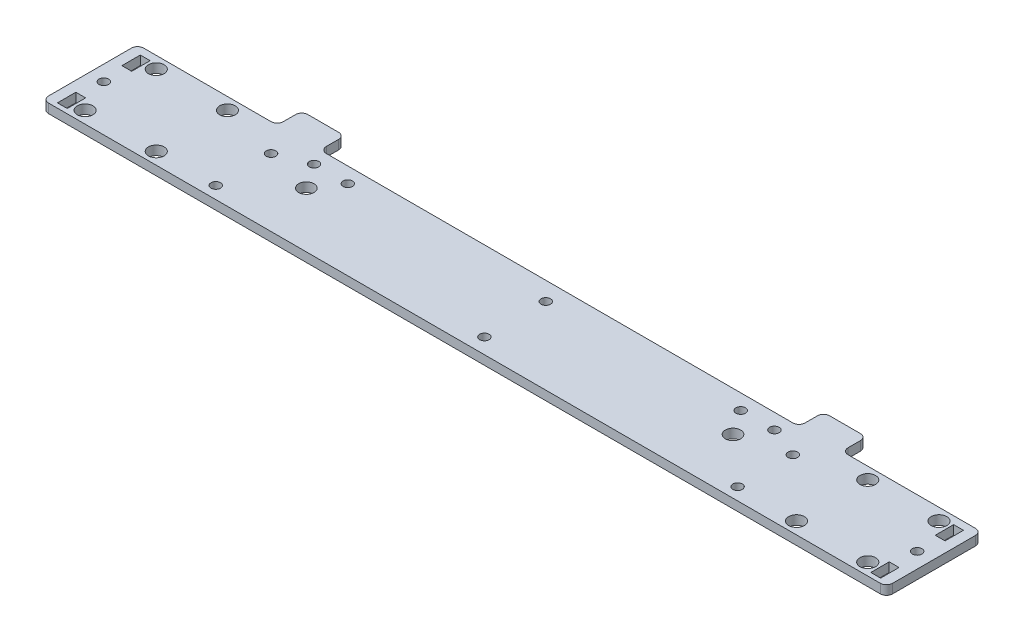
SolidWorks part; units mm, degrees
ref_plane "Alzado" through (0, 0, 0) normal (0, 0, 1) x (1, 0, 0)
ref_plane "Planta" through (0, 0, 0) normal (0, 1, 0) x (1, 0, 0)
ref_plane "Vista lateral" through (0, 0, 0) normal (1, 0, 0) x (0, 0, -1)
sketch "Croquis1" plane through (0, 0, 0) normal (0, 1, 0) x (1, 0, 0)
  line L0 (137.5, 31) -> (137.5, 0) construction
  line L1 (0, 0) -> (275, 0)
  line L2 (0, 0) -> (0, 31)
  line L3 (0, 31) -> (45.5, 31)
  line L4 (275, 0) -> (275, 31)
  line L5 (271.6, 1.5) -> (268.4, 1.5)
  line L6 (3.4, 28.5) -> (6.6, 28.5)
  line L7 (3.4, 28.5) -> (3.4, 22.5)
  line L8 (3.4, 22.5) -> (6.6, 22.5)
  line L9 (6.6, 28.5) -> (6.6, 22.5)
  line L10 (3.4, 7.5) -> (6.6, 7.5)
  line L11 (3.4, 7.5) -> (3.4, 1.5)
  line L12 (3.4, 1.5) -> (6.6, 1.5)
  line L13 (6.6, 7.5) -> (6.6, 1.5)
  line L14 (271.6, 7.5) -> (271.6, 1.5)
  line L15 (271.6, 7.5) -> (268.4, 7.5)
  line L16 (268.4, 7.5) -> (268.4, 1.5)
  line L17 (271.6, 22.5) -> (268.4, 22.5)
  line L18 (271.6, 28.5) -> (271.6, 22.5)
  line L19 (268.4, 28.5) -> (268.4, 22.5)
  line L20 (271.6, 28.5) -> (268.4, 28.5)
  line L21 (6.6, 31) -> (6.6, 0) construction
  line L22 (36.6, 31) -> (36.6, 0) construction
  line L23 (6.6, 0) -> (36.6, 31) construction
  line L24 (59.5, 31) -> (215.5, 31)
  line L25 (10, 27.1) -> (33.2, 27.1) construction
  line L26 (10, 27.1) -> (10, 3.9) construction
  line L27 (10, 3.9) -> (33.2, 3.9) construction
  line L28 (33.2, 27.1) -> (33.2, 3.9) construction
  line L29 (10, 27.1) -> (33.2, 3.9) construction
  line L30 (10, 3.9) -> (33.2, 27.1) construction
  line L32 (45.5, 31) -> (45.5, 39)
  line L33 (45.5, 39) -> (59.5, 39)
  line L34 (59.5, 31) -> (59.5, 39)
  line L35 (229.5, 31) -> (229.5, 39)
  line L36 (229.5, 39) -> (215.5, 39)
  line L37 (215.5, 31) -> (215.5, 39)
  line L38 (229.5, 31) -> (275, 31)
  line L39 (139, 31) -> (139, 0) construction
  line L40 (52.5, 39) -> (52.5, 0) construction
  line L41 (222.5, 39) -> (222.5, 0) construction
  line L42 (212.5, 26) -> (212.5, 8.2276) construction
  circle A0 centre (5, 15) radius 1.55
  circle A1 centre (270, 15) radius 1.55
  circle A2 centre (10, 27.1) radius 2.55
  circle A3 centre (33.2, 27.1) radius 2.55
  circle A4 centre (33.2, 3.9) radius 2.55
  circle A5 centre (10, 3.9) radius 2.55
  circle A6 centre (265, 3.9) radius 2.55
  circle A7 centre (241.8, 3.9) radius 2.55
  circle A8 centre (265, 27.1) radius 2.55
  circle A9 centre (241.8, 27.1) radius 2.55
  circle A10 centre (139, 25) radius 1.55
  circle A11 centre (139, 5) radius 1.55
  circle A12 centre (52.5, 22) radius 1.55
  circle A13 centre (52.5, 4) radius 1.55
  circle A14 centre (222.5, 22) radius 1.55
  circle A15 centre (222.5, 4) radius 1.55
  circle A16 centre (212.5, 26) radius 1.55
  circle A17 centre (62.5, 26) radius 1.55
  circle A18 centre (201.5, 26) radius 1.55
  circle A19 centre (73.5, 26) radius 1.55
  circle A20 centre (207, 18) radius 2.5
  circle A21 centre (68, 18) radius 2.5
  point P31 (21.6, 15.5)
  dimension "D8" = 3.1
  dimension "D17" = 5.1
  dimension "D21" = 3.1
  dimension "D22" = 6
  dimension "D25" = 3.1
  dimension "D26" = 18
  dimension "D27" = 4
  dimension "D28" = 3.1
  dimension "D31" = 11
  dimension "D32" = 5
  dimension "D1" = 31
  dimension "D2" = 275
  dimension "D3" = 3.4
  dimension "D4" = 6
  dimension "D5" = 6
  dimension "D6" = 3.2
  dimension "D7" = 3.2
  dimension "D9" = 3.4
  dimension "D10" = 5
  dimension "D11" = 15
  dimension "D12" = 7.5
  dimension "D13" = 1.5
  dimension "D14" = 30
  dimension "D15" = 23.2
  dimension "D16" = 23.2
  dimension "D18" = 8
  dimension "D19" = 14
  dimension "D20" = 45.5
  dimension "D23" = 20
  dimension "D24" = 139
  dimension "D29" = 5
  dimension "D30" = 10
  dimension "D33" = 8
  dimension "D34" = 5.5
extrude "Saliente-Extruir1" add sketch "Croquis1" along normal blind 3
fillet "Redondeo2" radius 2 12 edges at (275, 1.5, 0) (275, 1.5, -31) (229.5, 1.5, -31) (229.5, 1.5, -39) (215.5, 1.5, -39) (215.5, 1.5, -31) (59.5, 1.5, -31) (59.5, 1.5, -39) (0, 1.5, 0) (45.5, 1.5, -39) (45.5, 1.5, -31) (0, 1.5, -31)
